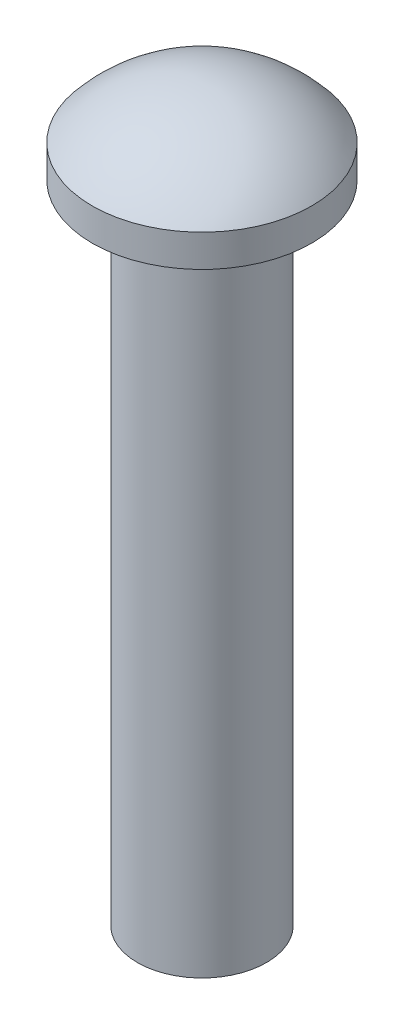
SolidWorks part; units mm, degrees
ref_plane "Front Plane" through (0, 0, 0) normal (0, 0, 1) x (1, 0, 0)
ref_plane "Top Plane" through (0, 0, 0) normal (0, 1, 0) x (1, 0, 0)
ref_plane "Right Plane" through (0, 0, 0) normal (1, 0, 0) x (0, 0, -1)
sketch "Sketch1" plane through (0, 0, 0) normal (0, 0, 1) x (1, 0, 0)
  line L0 (0, 0) -> (0, -22.184) construction
  line L2 (-1, 0) -> (-1.7, 0)
  line L3 (0, 0) -> (0, 1.3)
  line L5 (-1.7, 0) -> (-1.7, 0.5)
  line L7 (0, 0) -> (0, -10)
  line L8 (0, -10) -> (-1, -10)
  line L9 (-1, 0) -> (-1, -10)
  arc A0 (-1.7, 0.5) -> (0, 1.3) centre (0, -0.9062) cw
  dimension "D1" = 2
  dimension "D2" = 3.4
  dimension "D3" = 10
  dimension "D4" = 1.3
  dimension "D5" = 0.5
revolve "Revolve1" add sketch "Sketch1" angle 360 about L0
